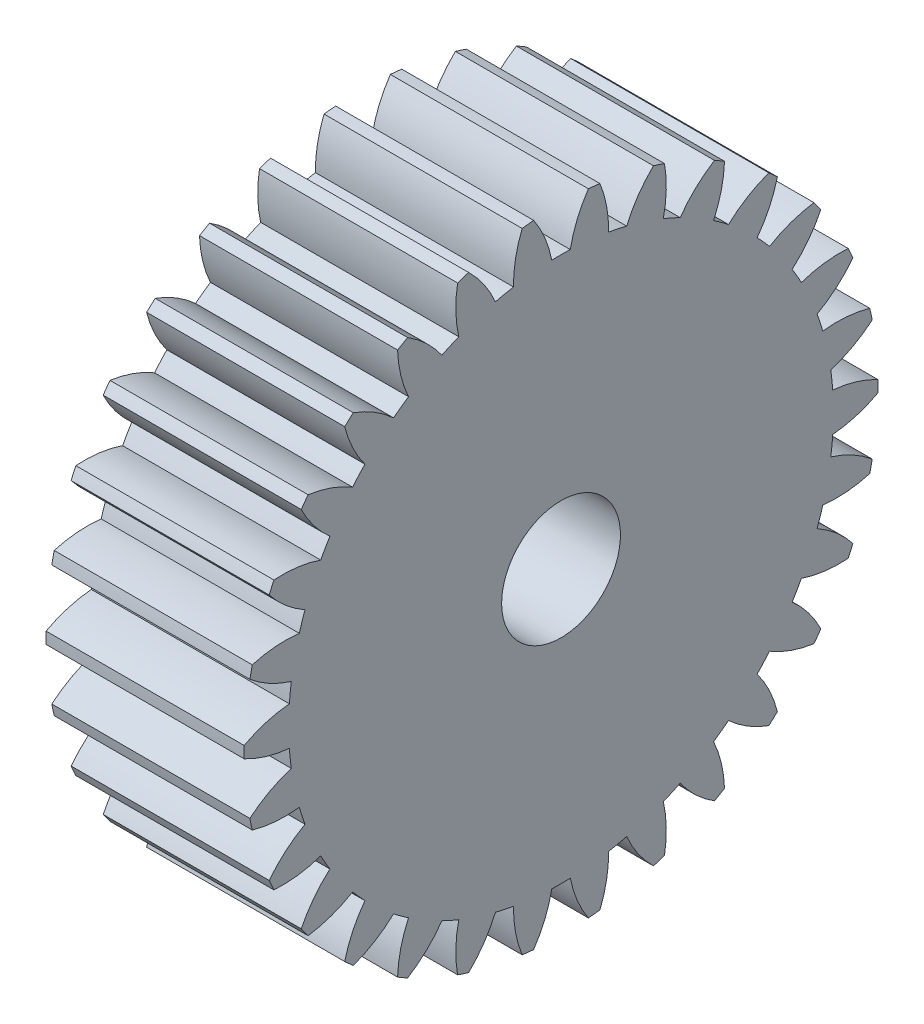
SolidWorks part; units mm, degrees
ref_plane "Plane1" through (0, 0, 0) normal (0, 0, 1) x (1, 0, 0)
ref_plane "Plane2" through (0, 0, 0) normal (0, 1, 0) x (1, 0, 0)
ref_plane "Plane3" through (0, 0, 0) normal (1, 0, 0) x (0, 0, -1)
sketch "HoldingSke" plane through (0, 0, 0) normal (0, 1, 0) x (1, 0, 0)
  line L0 (0, 0) -> (0.866, -0.5)
  line L1 (-15, 0) -> (100, 0) construction
  line L2 (0, 0) -> (-2.1039, 2.3779)
  line L3 (0, 0) -> (-11.863, 4.5341)
  line L4 (0, 0) -> (7.479, 4.318)
  line L5 (0, 0) -> (-16.8652, -6.2902)
  line L6 (0, 0) -> (-8.2896, -5.593)
  line L7 (-2.1039, 2.3779) -> (1.7706, 19.956)
  line L8 (-76.2, 54.61) -> (-75.2, 54.61)
  line L9 (-71.009, 38.7566) -> (-53.1078, 45.2721)
  line L10 (-76.2, 71.12) -> (104.1128, 71.12)
  line L11 (0, 0) -> (-10, 0)
  line L12 (-76.2, 101.6) -> (-76.162, 101.6)
  line L13 (24.9733, 27.94) -> (52.9518, 28.4284)
  line L14 (24.9733, 27.94) -> (24.9743, 27.94)
  line L15 (24.9733, 27.94) -> (100.4006, 29.5858)
  line L16 (-63.627, -1) -> (-12.827, -1)
  circle A0 centre (0, 0) radius 3
  circle A1 centre (0, 0) radius 12.5
  circle A2 centre (0, 0) radius 12.5
  circle A3 centre (0, 0) radius 3
  dimension "MHD" = 25
  dimension "Hub_dia" = 25
  dimension "Bore" = 6
  dimension "MBD" = 6
  dimension "Num_teeth" = 30
  dimension "Pitch" = 1
  dimension "Overall_len" = 18
  dimension "Show_teeth" = 30
  dimension "Thickness" = 10
  dimension "OAL" = 18.0001
  dimension "T_dim" = 1
  dimension "Ap" = 20
  dimension "H" = 19.05
  dimension "Pitch_radius" = 180.3128
  dimension "Width" = 10
  dimension "Backlash" = 0.038
  dimension "Addendum_fac" = 1
  dimension "Dedendum_fac" = 1.25
  dimension "Clearance_fac" = 0.25
  dimension "Dedendum_add" = 0.001
  dimension "Module" = 1
sketch "BasProSke" plane through (0, 0, 0) normal (0, 1, 0) x (1, 0, 0)
  line L0 (-10, 0) -> (60, 0) construction
  line L1 (0, 0) -> (0, 16)
  line L2 (0, 0) -> (10, 0)
  line L3 (10, 0) -> (10, 16)
  line L4 (10, 16) -> (0, 16)
  dimension "Thickness" = 10
  dimension "Diameter" = 32
revolve "Base-Revolve" add sketch "BasProSke" angle 360 about L0
sketch "TooCutSke" plane through (0, 0, 0) normal (1, 0, 0) x (0, 0, -1)
  line L1 (0, 0) -> (0, 107) construction
  line L2 (0, 0) -> (-0.8515, 14.9758) construction
  line L3 (0, 0) -> (-3.1323, 29.8014) construction
  line L4 (-0.8515, 14.9758) -> (-1.5661, 14.9007) construction
  arc A0 (0.4664, 13.7411) -> (-0.4664, 13.7411) centre (0, 0) ccw
  arc A1 (1.3975, 15.9644) -> (-1.3975, 15.9644) centre (0, 0) ccw
  circle A2 centre (0, 0) radius 15 construction
  circle A3 centre (0, 0) radius 14.0954 construction
  arc A4 (-0.4664, 13.7411) -> (-1.3975, 15.9644) centre (-6.3534, 12.5823) ccw
  arc A5 (1.3975, 15.9644) -> (0.4664, 13.7411) centre (6.3534, 12.5823) ccw
  dimension "Root_dia" = 27.498
  dimension "Overcut_dia" = 32.0508
  dimension "Pitch_dia" = 30
  dimension "Base_dia" = 28.1908
  dimension "Flank_rad" = 6
  dimension "Half_ang" = 6
  dimension "Half_CT" = 0.7185
extrude "ToothCut" cut sketch "TooCutSke" along normal through all
fillet "Breaks" [suppressed] radius 0.02
fillet "RootFillets" [suppressed] radius 0.251
pattern_circular "TeethCuts" count 30 every 12 about axis through (-10, 0, 0) along (1, 0, 0) of "ToothCut", "RootFillets", "Breaks"
sketch "HubNeaOneSke" plane through (0, 0, 0) normal (-1, 0, 0) x (0, 0, 1)
  circle A0 centre (0, 0) radius 12.5
  dimension "Diameter" = 25
extrude "HubNearOne" add sketch "HubNeaOneSke" along normal blind 8.0001
sketch "HubNeaBotSke" plane through (0, 0, 0) normal (-1, 0, 0) x (0, 0, 1)
  circle A0 centre (0, 0) radius 12.5
  dimension "Diameter" = 25
extrude "HubNearBoth" [suppressed] add sketch "HubNeaBotSke" along normal blind 4
ref_plane "FarPln" through (10, 0, 0) normal (1, 0, 0) x (0, 0, -1)
sketch "HubFarSke" plane through (10, 0, 0) normal (1, 0, 0) x (0, 0, -1)
  circle A0 centre (0, 0) radius 12.5
  dimension "Diameter" = 25
extrude "HubFar" [suppressed] add sketch "HubFarSke" along normal blind 4
sketch "BorSke" plane through (0, 0, 0) normal (1, 0, 0) x (0, 0, -1)
  circle A0 centre (0, 0) radius 3
  dimension "Diameter" = 6
extrude "Bore" cut sketch "BorSke" along normal mid plane 36.0001
sketch "KeySke" plane through (0, 0, 0) normal (1, 0, 0) x (0, 0, -1)
  line L0 (-1, 0) -> (-1, 4)
  line L1 (-1, 4) -> (1, 4)
  line L2 (1, 4) -> (1, 0)
  line L3 (0, 0) -> (0, 34) construction
  line L4 (-1, 0) -> (1, 0)
  dimension "Offset" = 4
  dimension "Width" = 2
extrude "Keyway" [suppressed] cut sketch "KeySke" along normal mid plane 36.0001
pattern_circular "Keyway2" [suppressed] count 2 every 90 about axis through (-10, 0, 0) along (1, 0, 0)
sketch "Sketch1" plane through (-8.0001, 0, 0) normal (-1, 0, 0) x (0, 0, 1)
  circle A1 centre (0, 0) radius 12.5
  circle A2 centre (0, 0) radius 12.5
  dimension "D1" = 0
extrude "Cut-Extrude1" cut sketch "Sketch1" against normal up to surface (8.0001 mm away) up to face at (0, 0, -12.5)
equation "' \"Module@HoldingSke\" = 6.35"
equation "' \"Num_teeth@HoldingSke\" = 12"
equation "' \"Ap@HoldingSke\" =  20"
equation "' \"Ap@HoldingSke\" = 20"
equation "' \"Width@HoldingSke\" = 0.5 * 25.4"
equation "' \"Hub_dia@HoldingSke\"= 1 * 25.4"
equation "' \"Hub_dia@HoldingSke\" = 1 * 25.4"
equation "' \"Overall_len@HoldingSke\" = 1.0 * 25.4"
equation "' \"Bore@HoldingSke\" = 0.75 * 25.4"
equation "' \"T_dim@HoldingSke\" = 0.1 * 25.4"
equation "' \"Width@KeySke\" = 0.25 * 25.4"
equation "' \"Show_teeth@HoldingSke\" = 13"
equation "' \"Backlash@HoldingSke\" = 0.009 * 25.4"
equation "' \"Addendum_fac@HoldingSke\" = 1.0"
equation "' \"Dedendum_fac@HoldingSke\" = 1.25"
equation "' \"Dedendum_add@HoldingSke\" = 0.00005 * 25.4"
equation "' \"Clearance_fac@HoldingSke\" = 0.25"
equation "\"Pitch@HoldingSke\" = 1 / \"Module@HoldingSke\""
equation "\"Overcut_dia@TooCutSke\" = (\"Num_teeth@HoldingSke\" + 2 * \"Addendum_fac@HoldingSke\") / \"Pitch@HoldingSke\" + 0.002 * 25.4"
equation "\"Pitch_dia@TooCutSke\" = \"Num_teeth@HoldingSke\" / \"Pitch@HoldingSke\""
equation "\"Base_dia@TooCutSke\" = \"Num_teeth@HoldingSke\" / \"Pitch@HoldingSke\" * cos((\"Ap@HoldingSke\"  * 3.14159265 / 180))"
equation "\"Root_dia@TooCutSke\" = (\"Num_teeth@HoldingSke\" + 2) / \"Pitch@HoldingSke\" - 2 * (\"Addendum_fac@HoldingSke\" + \"Dedendum_fac@HoldingSke\") / \"Pitch@HoldingSke\" - \"Dedendum_add@HoldingSke\" * 2"
equation "\"Half_ang@TooCutSke\" = 180 / \"Num_teeth@HoldingSke\""
equation "\"Half_CT@TooCutSke\" = \"Num_teeth@HoldingSke\" / \"Pitch@HoldingSke\" * sin((3.14159265 / 2 / \"Num_teeth@HoldingSke\")) / 2 - 7 * \"Backlash@HoldingSke\" / 4"
equation "\"Flank_rad@TooCutSke\" = \"Num_teeth@HoldingSke\" / \"Pitch@HoldingSke\" / 5"
equation "\"Radius@RootFillets\" = \"Clearance_fac@HoldingSke\" / \"Pitch@HoldingSke\" + \"Dedendum_add@HoldingSke\""
equation "\"Break_rad@Breaks\" = 0.02 / \"Pitch@HoldingSke\""
equation "\"Thickness@HoldingSke\" = \"Width@HoldingSke\""
equation "\"OAL@HoldingSke\" = \"Thickness@HoldingSke\""
equation "\"MHD@HoldingSke\" = (\"Num_teeth@HoldingSke\" + 2) / \"Pitch@HoldingSke\" - 2 * (\"Addendum_fac@HoldingSke\" + \"Dedendum_fac@HoldingSke\")  / \"Pitch@HoldingSke\" - \"Dedendum_add@HoldingSke\" * 2"
equation "\"MBD@HoldingSke\" = (\"Num_teeth@HoldingSke\" + 2) / \"Pitch@HoldingSke\" - 2 * (\"Addendum_fac@HoldingSke\" + \"Dedendum_fac@HoldingSke\")  / \"Pitch@HoldingSke\" - \"Dedendum_add@HoldingSke\" * 2 - 0.002 * 25.4"
equation "\"MHD@HoldingSke\" = ((sgn( \"MHD@HoldingSke\" - \"Hub_dia@HoldingSke\" )-1)*( \"MHD@HoldingSke\" - \"Hub_dia@HoldingSke\" ))/-2+ \"Hub_dia@HoldingSke\""
equation "\"MBD@HoldingSke\" = ((sgn( \"MBD@HoldingSke\" - \"Bore@HoldingSke\" )-1)*( \"MBD@HoldingSke\" - \"Bore@HoldingSke\" ))/-2+ \"Bore@HoldingSke\""
equation "\"OAL@HoldingSke\" = ((sgn( \"OAL@HoldingSke\" - \"Overall_len@HoldingSke\" )+1)*( \"OAL@HoldingSke\" - \"Overall_len@HoldingSke\" ))/2 + \"Overall_len@HoldingSke\" + 0.000002 * 25.4"
equation "\"Num_teeth@TeethCuts\" = int( \"Show_teeth@HoldingSke\" ) + 1"
equation "\"Num_teeth@TeethCuts\" = ((sgn( \"Num_teeth@TeethCuts\" - \"Num_teeth@HoldingSke\" )-1)*( \"Num_teeth@TeethCuts\" - \"Num_teeth@HoldingSke\" ))/-2+ \"Num_teeth@HoldingSke\""
equation "\"Num_teeth@TeethCuts\" = ((sgn( \"Num_teeth@TeethCuts\" - 2.0)+1)*( \"Num_teeth@TeethCuts\" - 2.0))/2 +2.0"
equation "\"Angle@TeethCuts\" = 360.0 / \"Num_teeth@HoldingSke\""
equation "\"Diameter@BasProSke\" = (\"Num_teeth@HoldingSke\" + 2 * \"Addendum_fac@HoldingSke\") / \"Pitch@HoldingSke\""
equation "\"Thickness@BasProSke\"  = \"Thickness@HoldingSke\""
equation "' \"Fillet_rad@BasProSke\" =  \"Thickness@HoldingSke\" * 0.05"
equation "' \"Fillet_rad@BasProSke\" = \"Thickness@HoldingSke\" * 0.05"
equation "\"MHD@HoldingSke\" = ((sgn( \"MHD@HoldingSke\" - \"Root_dia@TooCutSke\" )-1)*( \"MHD@HoldingSke\" - \"Root_dia@TooCutSke\" ))/-2+ \"Root_dia@TooCutSke\""
equation "\"Diameter@HubNeaOneSke\" = \"MHD@HoldingSke\""
equation "\"Length@HubNearOne\" = \"OAL@HoldingSke\" - \"Thickness@BasProSke\""
equation "\"Diameter@HubNeaBotSke\" = \"MHD@HoldingSke\""
equation "\"Length@HubNearBoth\" = ( \"OAL@HoldingSke\" - \"Thickness@BasProSke\" ) / 2.0"
equation "\"Thickness@FarPln\" = \"Thickness@BasProSke\""
equation "\"Diameter@HubFarSke\" = \"MHD@HoldingSke\""
equation "\"Length@HubFar\" = ( \"OAL@HoldingSke\" - \"Thickness@BasProSke\" ) / 2.0"
equation "\"Diameter@BorSke\" = \"MBD@HoldingSke\""
equation "\"D1@Bore\" = \"OAL@HoldingSke\" * 2.0"
equation "\"D1@Keyway\" = \"OAL@HoldingSke\" * 2.0"
equation "\"Offset@KeySke\" = \"T_dim@HoldingSke\" + \"MBD@HoldingSke\" / 2.0"
